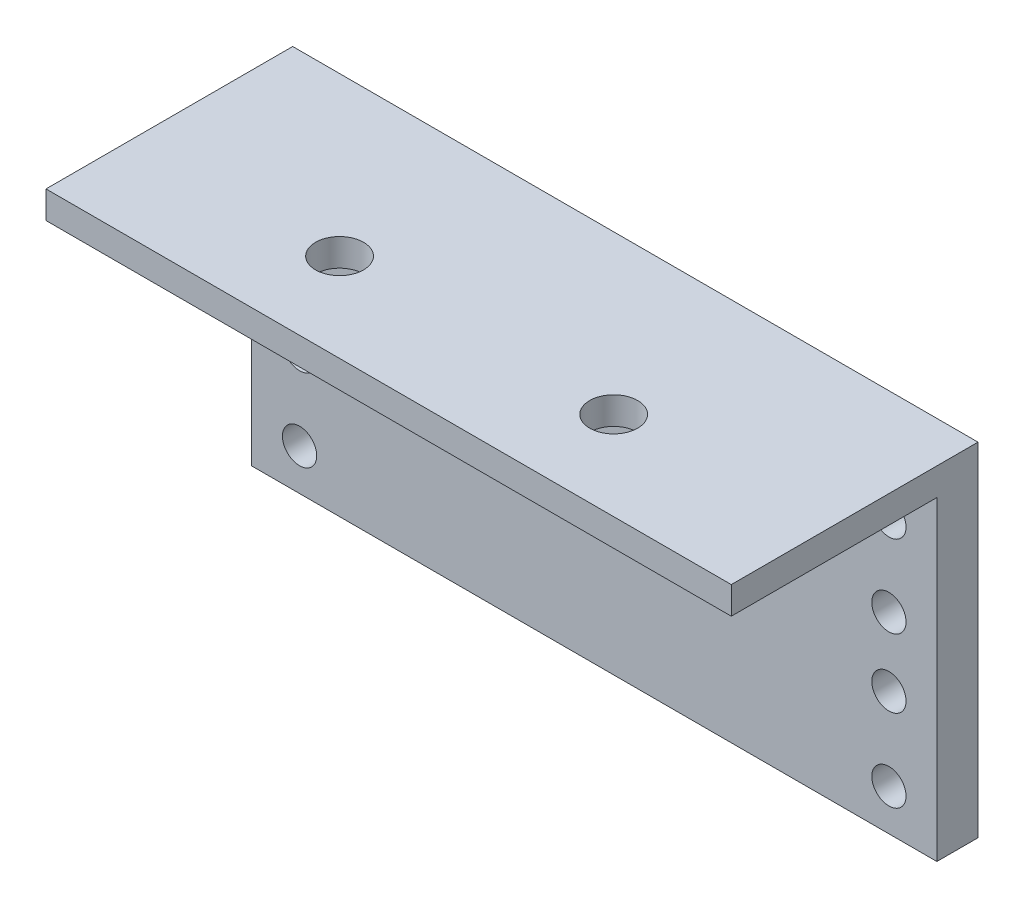
SolidWorks part; units mm, degrees
ref_plane "Front Plane" through (0, 0, 0) normal (0, 0, 1) x (1, 0, 0)
ref_plane "Top Plane" through (0, 0, 0) normal (0, 1, 0) x (1, 0, 0)
ref_plane "Right Plane" through (0, 0, 0) normal (1, 0, 0) x (0, 0, -1)
sketch "Sketch1" plane through (0, 0, 0) normal (0, 0, 1) x (1, 0, 0)
  line L1 (0, 0) -> (-50, 0)
  line L2 (0, 0) -> (0, 25)
  line L3 (0, 25) -> (-50, 25)
  line L4 (-50, 0) -> (-50, 25)
  dimension "D1" = 50
  dimension "D2" = 25
extrude "Boss-Extrude1" add sketch "Sketch1" along normal blind 3
sketch "Sketch3" plane through (0, 0, 3) normal (0, 0, 1) x (1, 0, 0)
  line L0 (0, -55) -> (0, 55) construction
  line L1 (-50, 25) -> (0, 25)
  line L2 (-50, 25) -> (-50, 23)
  line L3 (-50, 23) -> (0, 23)
  line L4 (0, 25) -> (0, 23)
  dimension "D1" = 2
extrude "Boss-Extrude2" add sketch "Sketch3" along normal blind 15
sketch "Sketch5" plane through (0, 0, 3) normal (0, 0, 1) x (1, 0, 0)
  line L0 (-48.7769, 17.0092) -> (-2.8518, 17.0092) construction
  line L1 (-47.8229, 6.0092) -> (-3.5001, 6.0092) construction
  circle A0 centre (-46.5001, 20.0092) radius 1.25
  circle A3 centre (-46.5001, 3.0092) radius 1.25
  circle A4 centre (-3.5001, 20.0092) radius 1.25
  circle A5 centre (-3.5001, 3.0092) radius 1.25
  circle A6 centre (-3.5001, 14.0092) radius 1.25
  circle A7 centre (-46.5001, 14.0092) radius 1.25
  circle A8 centre (-3.5001, 9.0092) radius 1.25
  circle A9 centre (-46.5001, 9.0092) radius 1.25
  dimension "D1" = 43
  dimension "D2" = 2.5
  dimension "D3" = 17
  dimension "D4" = 17
  dimension "D5" = 3
  dimension "D6" = 3
extrude "Cut-Extrude1" cut sketch "Sketch5" against normal blind 15
sketch "Sketch6" plane through (0, 25, 0) normal (0, 1, 0) x (1, 0, 0)
  circle A0 centre (-35.0461, -11.5352) radius 1.75
  circle A1 centre (-15.0461, -11.5352) radius 1.75
  dimension "D1" = 3.5
  dimension "D2" = 20
extrude "Cut-Extrude2" cut sketch "Sketch6" against normal blind 15
